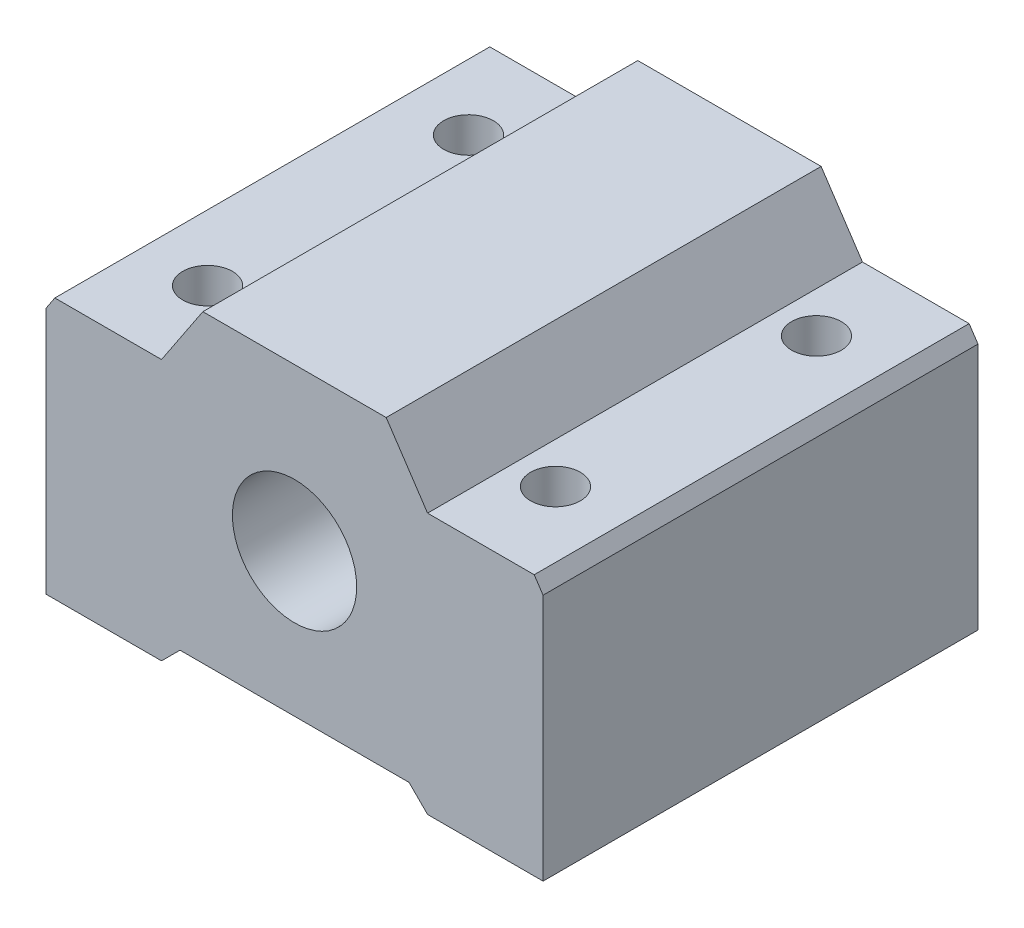
SolidWorks part; units mm, degrees
ref_plane "Front Plane" through (0, 0, 0) normal (0, 0, 1) x (1, 0, 0)
ref_plane "Top Plane" through (0, 0, 0) normal (0, 1, 0) x (1, 0, 0)
ref_plane "Right Plane" through (0, 0, 0) normal (1, 0, 0) x (0, 0, -1)
sketch "Sketch1" plane through (0, 0, 0) normal (0, 0, 1) x (1, 0, 0)
  line L0 (-7.3763, 13) -> (-10.7049, 8)
  line L1 (-20, -13) -> (-12.1932, -13)
  line L2 (-20, -13) -> (-20, 6.9293)
  line L3 (-7.3763, 13) -> (7.3763, 13)
  line L4 (20, -13) -> (20, 6.9293)
  line L5 (12.1932, -13) -> (20, -13)
  line L7 (-10.7049, 8) -> (-19.2872, 8)
  line L8 (-19.2872, 8) -> (-20, 6.9293)
  line L9 (0, 14) -> (0, -14) construction
  line L10 (7.3763, 13) -> (10.7049, 8)
  line L11 (10.7049, 8) -> (19.2872, 8)
  line L12 (19.2872, 8) -> (20, 6.9293)
  line L13 (-12.1932, -13) -> (-10.7049, -13)
  line L14 (-9.2165, -11.5117) -> (9.2165, -11.5117)
  line L15 (-10.7049, -13) -> (-9.2165, -11.5117)
  line L17 (12.1932, -13) -> (10.7049, -13)
  line L18 (10.7049, -13) -> (9.2165, -11.5117)
  circle A0 centre (0, 0) radius 5
  point P0 (0, 0)
  dimension "D3" = 21
  dimension "D8" = 13
  dimension "D1" = 40
  dimension "D2" = 26
  dimension "D4" = 8.5824
  dimension "D5" = 8.5824
  dimension "D6" = 14.7527
  dimension "D7" = 18.4331
extrude "Boss-Extrude1" add sketch "Sketch1" along normal blind 35
sketch "Sketch2" plane through (0, -13, 0) normal (0, -1, 0) x (1, 0, 0)
  line L0 (0, 35) -> (0, 0) construction
  line L1 (-9.2165, 35) -> (9.2165, 35) construction
  line L2 (0, 17.5) -> (-20, 17.5) construction
  line L3 (-20, 35) -> (-20, 0) construction
  line L5 (-14, 7) -> (14, 7) construction
  line L6 (-14, 7) -> (-14, 28) construction
  line L7 (-14, 28) -> (14, 28) construction
  line L8 (14, 7) -> (14, 28) construction
  line L9 (-14, 7) -> (14, 28) construction
  line L10 (-14, 28) -> (14, 7) construction
  circle A0 centre (-14, 28) radius 2
  circle A1 centre (14, 28) radius 2
  circle A2 centre (14, 7) radius 2
  circle A3 centre (-14, 7) radius 2
  dimension "D1" = 28
  dimension "D2" = 21
extrude "Cut-Extrude1" cut sketch "Sketch2" against normal up to next
